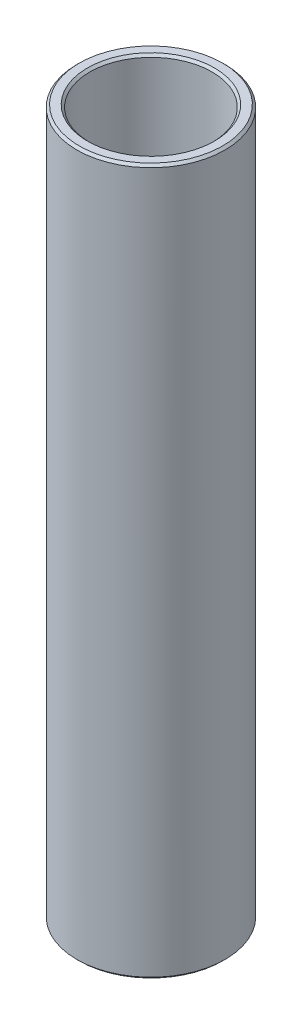
SolidWorks part; units mm, degrees
ref_plane "Front Plane" through (0, 0, 0) normal (0, 0, 1) x (1, 0, 0)
ref_plane "Top Plane" through (0, 0, 0) normal (0, 1, 0) x (1, 0, 0)
ref_plane "Right Plane" through (0, 0, 0) normal (1, 0, 0) x (0, 0, -1)
sketch "Sketch1" plane through (0, 0, 0) normal (0, 0, 1) x (1, 0, 0)
  line L0 (0, 7.4068) -> (0, -7.4068) construction
  line L1 (3.3, 19.05) -> (3.3, -19.05)
  line L2 (3.3, -19.05) -> (4, -19.05)
  line L3 (4, -19.05) -> (4, 19.05)
  line L4 (4, 19.05) -> (3.3, 19.05)
  point P7 (3.3, 0)
  dimension "D1" = 38.1
  dimension "D2" = 6.6
  dimension "D3" = 8
revolve "Revolve1" add sketch "Sketch1" angle 360 about L0
chamfer "Chamfer1" distance 0.127 angle 45 4 edges at (0, -19.05, 3.3) (0, -19.05, 4) (0, 19.05, 4) (0, 19.05, 3.3)
